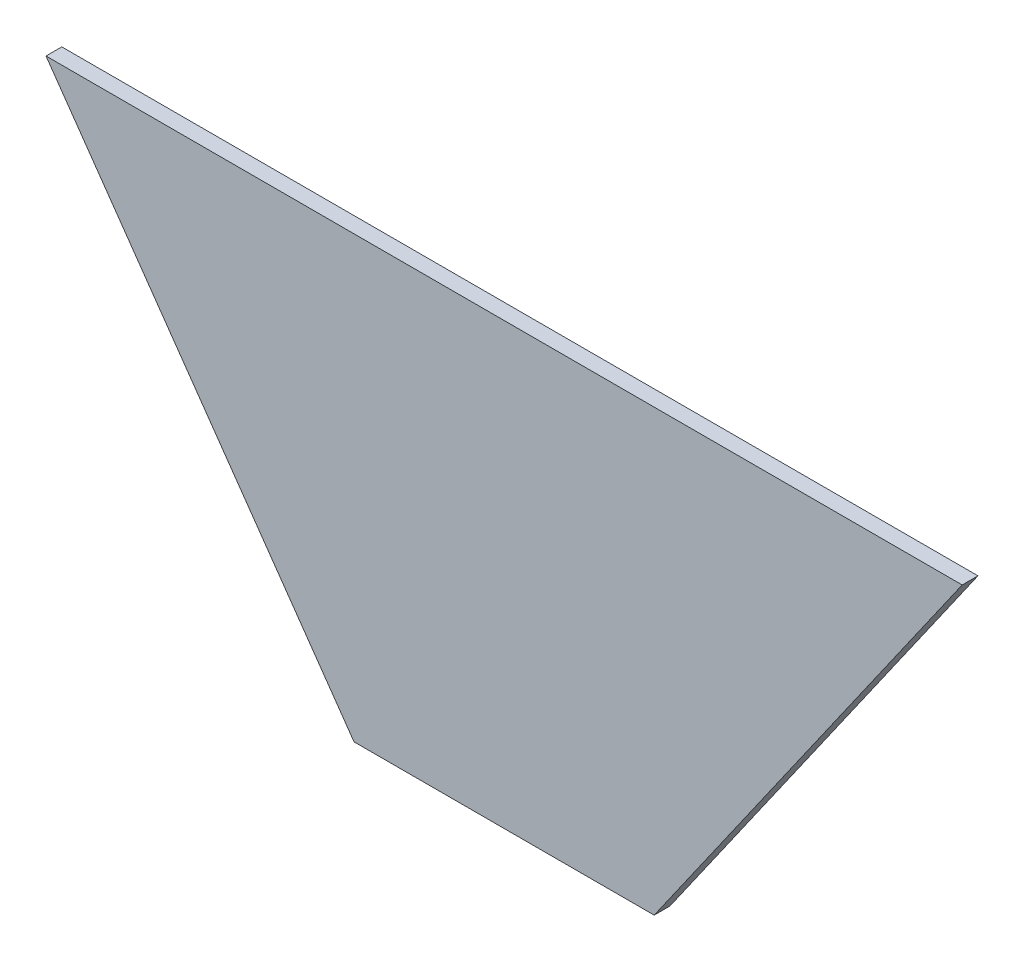
SolidWorks part; units mm, degrees
ref_plane "Front Plane" through (0, 0, 0) normal (0, 0, 1) x (1, 0, 0)
ref_plane "Top Plane" through (0, 0, 0) normal (0, 1, 0) x (1, 0, 0)
ref_plane "Right Plane" through (0, 0, 0) normal (1, 0, 0) x (0, 0, -1)
sketch "Sketch2" plane through (0, 0, 0) normal (0, 0, 1) x (1, 0, 0)
  line L0 (-95, 0) -> (95, 0)
  line L1 (95, 0) -> (290, 278.5229)
  line L2 (290, 278.5229) -> (-290, 278.5229)
  line L3 (-290, 278.5229) -> (-95, 0)
  point P3 (0, 0)
  dimension "D1" = 190
  dimension "D2" = 580
  dimension "D3" = 340
  dimension "D4" = 340
extrude "Boss-Extrude1" add sketch "Sketch2" along normal blind 10
